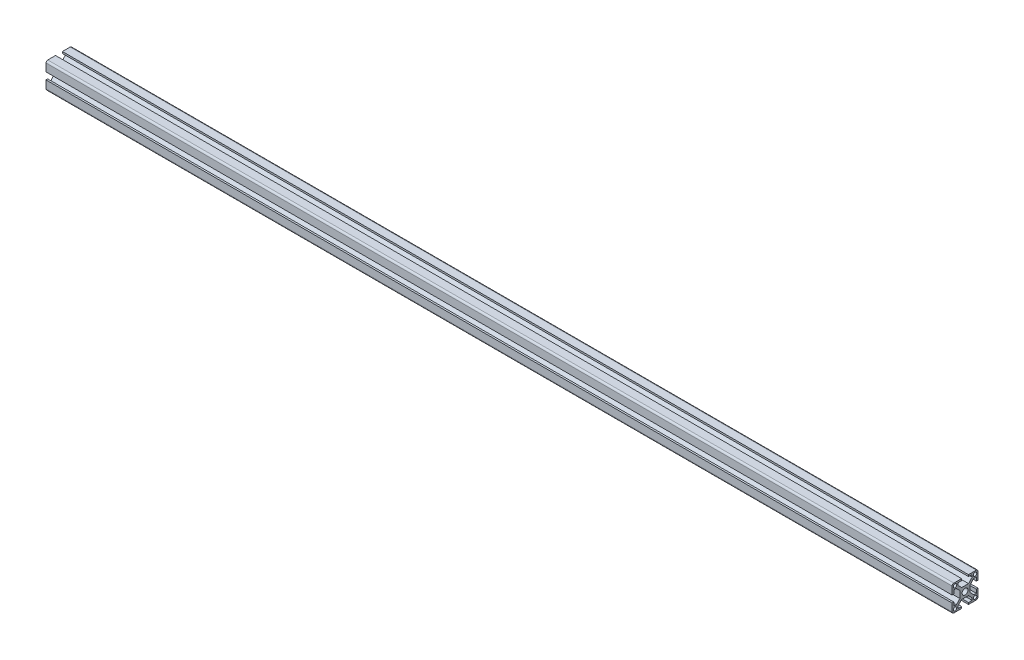
SolidWorks part; units mm, degrees
ref_plane "Front Plane" through (0, 0, 0) normal (0, 0, 1) x (1, 0, 0)
ref_plane "Top Plane" through (0, 0, 0) normal (0, 1, 0) x (1, 0, 0)
ref_plane "Right Plane" through (0, 0, 0) normal (1, 0, 0) x (0, 0, -1)
sketch "Sketch1" plane through (0, 0, 0) normal (0, 0, 1) x (1, 0, 0)
  line L0 (-343.691, 0) -> (706.309, 0)
  dimension "D1" = 1050
other "New alum ALUM3BY3(1)"
ref_plane "Plane1" through (-343.691, 0, 0) normal (1, 0, 0) x (0, 1, 0)
sketch "Sketch11" plane through (-343.691, 0, 0) normal (1, 0, 0) x (0, 1, 0)
  line L0 (0, -11.5423) -> (0, 11.5423) construction
  line L1 (13.3052, 0) -> (-13.3052, 0) construction
  line L2 (-4, 6) -> (4, 6)
  line L3 (4, 6) -> (8.25, 10.1061)
  line L4 (8.25, 10.1061) -> (8.25, 13)
  line L5 (8.25, 13) -> (4, 13)
  line L6 (4, 13) -> (4, 15)
  line L7 (4, 15) -> (13, 15)
  line L8 (15, 13) -> (15, 4)
  line L9 (15, 4) -> (13, 4)
  line L10 (13, 4) -> (13, 8.25)
  line L11 (13, 8.25) -> (10.3989, 8.25)
  line L12 (6, 4) -> (10.3989, 8.25)
  line L13 (6, 4) -> (6, -4)
  line L14 (-4, 15) -> (-13, 15)
  line L15 (-6, 4) -> (-6, -4)
  line L16 (-6, 4) -> (-10.3989, 8.25)
  line L17 (-13, 8.25) -> (-10.3989, 8.25)
  line L18 (-13, 4) -> (-13, 8.25)
  line L19 (-15, 4) -> (-13, 4)
  line L20 (-15, 13) -> (-15, 4)
  line L21 (-4, 13) -> (-4, 15)
  line L22 (-8.25, 13) -> (-4, 13)
  line L23 (-8.25, 10.1061) -> (-8.25, 13)
  line L24 (-4, 6) -> (-8.25, 10.1061)
  line L25 (-4, -15) -> (-13, -15)
  line L26 (-15, -4) -> (-13, -4)
  line L27 (-15, -13) -> (-15, -4)
  line L28 (-4, -13) -> (-4, -15)
  line L29 (-8.25, -13) -> (-4, -13)
  line L30 (-8.25, -10.1061) -> (-8.25, -13)
  line L31 (8.25, -10.1061) -> (8.25, -13)
  line L32 (8.25, -13) -> (4, -13)
  line L33 (4, -13) -> (4, -15)
  line L34 (4, -15) -> (13, -15)
  line L35 (15, -13) -> (15, -4)
  line L36 (-4, -6) -> (-8.25, -10.1061)
  line L37 (-13, -4) -> (-13, -8.25)
  line L38 (-13, -8.25) -> (-10.3989, -8.25)
  line L39 (-6, -4) -> (-10.3989, -8.25)
  line L40 (6, -4) -> (10.3989, -8.25)
  line L41 (13, -8.25) -> (10.3989, -8.25)
  line L42 (13, -4) -> (13, -8.25)
  line L43 (15, -4) -> (13, -4)
  line L44 (4, -6) -> (8.25, -10.1061)
  line L45 (-4, -6) -> (4, -6)
  circle A1 centre (0, 0) radius 3.4
  circle A2 centre (11.6, 11.6) radius 2
  circle A3 centre (-11.6, 11.6) radius 2
  circle A4 centre (11.6, -11.6) radius 2
  circle A5 centre (-11.6, -11.6) radius 2
  arc A6 (-13, 15) -> (-15, 13) centre (-13, 13) ccw
  arc A7 (-13, -15) -> (-15, -13) centre (-13, -13) cw
  arc A8 (13, -15) -> (15, -13) centre (13, -13) ccw
  arc A9 (13, 15) -> (15, 13) centre (13, 13) cw
  point P3 (0, 0)
  point P4 (0, 0)
  point P8 (0, 0)
  point P39 (0, 6)
  point P55 (6, 0)
  point P56 (-6, 0)
  point P63 (0, -6)
  point P68 (-15, 15)
  point P71 (-15, -15)
  point P74 (15, -15)
  point P77 (15, 15)
  dimension "D1" = 6.8
  dimension "D2" = 4
  dimension "D11" = 4
  dimension "D17" = 2
  dimension "D3" = 4
  dimension "D4" = 8.25
  dimension "D5" = 8.25
  dimension "D6" = 15
  dimension "D7" = 15
  dimension "D8" = 2
  dimension "D9" = 2
  dimension "D10" = 6
  dimension "D12" = 7
  dimension "D13" = 4.25
  dimension "D14" = 4.25
  dimension "D15" = 6
  dimension "D16" = 6
  dimension "D18" = 23.2
  dimension "D19" = 23.2
sketch "Sketch12" plane through (0, 0, 6) normal (0, 0, 1) x (1, 0, 0)
  line L0 (-343.691, 0) -> (512.4326, 0) construction
  line L1 (-343.691, 4) -> (-343.691, -4) construction
  circle A0 centre (-268.691, 0) radius 2.5
  circle A1 centre (-168.691, 0) radius 2.5
  circle A2 centre (-78.731, 0) radius 2.5
  dimension "D1" = 5
  dimension "D2" = 75
  dimension "D3" = 100
  dimension "D4" = 89.96
extrude "Cut-Extrude1" cut sketch "Sketch12" against normal through all
